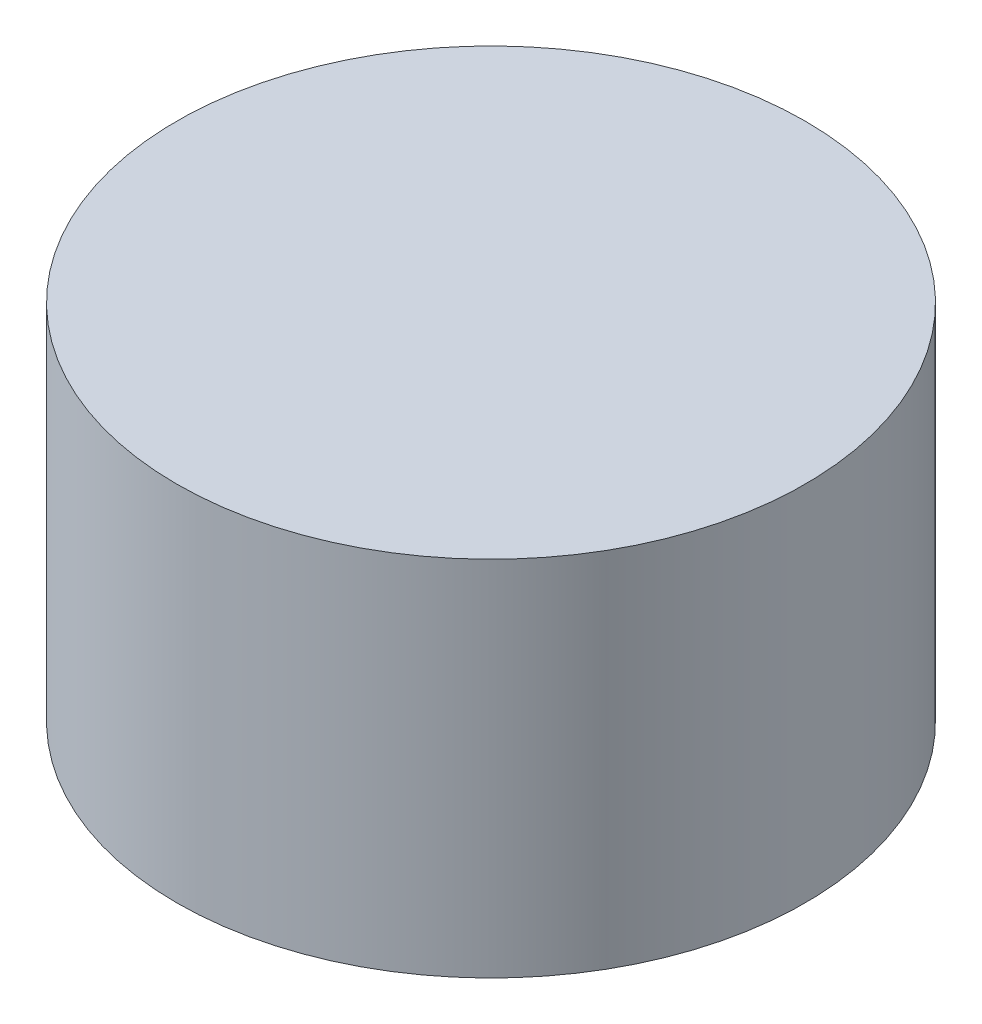
SolidWorks part; units mm, degrees
ref_plane "Front Plane" through (0, 0, 0) normal (0, 0, 1) x (1, 0, 0)
ref_plane "Top Plane" through (0, 0, 0) normal (0, 1, 0) x (1, 0, 0)
ref_plane "Right Plane" through (0, 0, 0) normal (1, 0, 0) x (0, 0, -1)
sketch "Sketch1" plane through (0, 0, 0) normal (0, 1, 0) x (1, 0, 0)
  circle A0 centre (0, 0) radius 33.02
  dimension "D1" = 66.04
extrude "Boss-Extrude1" add sketch "Sketch1" along normal blind 38.1
